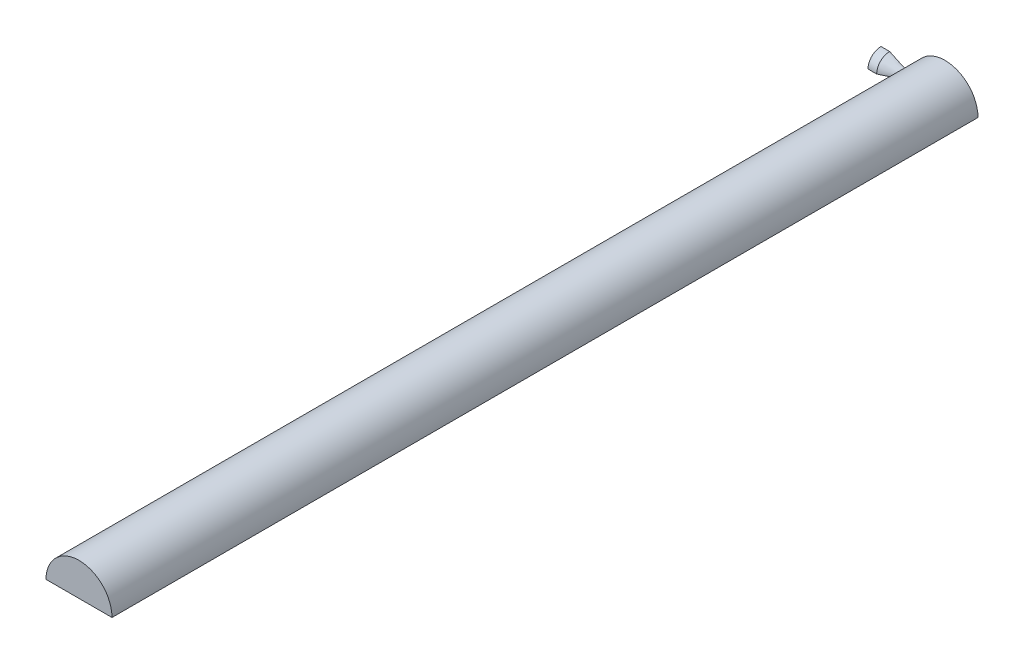
SolidWorks part; units mm, degrees
ref_plane "Front Plane" through (0, 0, 0) normal (0, 0, 1) x (1, 0, 0)
ref_plane "Top Plane" through (0, 0, 0) normal (0, 1, 0) x (1, 0, 0)
ref_plane "Right Plane" through (0, 0, 0) normal (1, 0, 0) x (0, 0, -1)
sketch "Sketch2" plane through (0, 0, 0) normal (0, 0, 1) x (1, 0, 0)
  line L0 (-0.6542, 15.02) -> (-10.6542, 15.02)
  line L1 (0, 0) -> (25.4, 0)
  line L3 (0, 0) -> (-10.6542, 0)
  line L4 (-10.6542, 15.02) -> (-10.6542, 0)
  line L5 (25.4, 4.5) -> (35.4, 4.5)
  line L6 (35.4, 4.5) -> (35.4, 0)
  line L7 (35.4, 0) -> (25.4, 0)
  spline S0 degree 4 poles (-3.1933, 16.2453) (-2.6483, 15.9818) (-1.017, 15.1947) (-0.2611, 14.8302) (2.741, 13.3865) (4.3471, 12.6191) (6.7016, 11.496) (8.6069, 10.5959) (10.7909, 9.5706) (12.8108, 8.6376) (14.9441, 7.6698) (16.9508, 6.7919) (18.7556, 6.0442) (20.2388, 5.4862) (21.3942, 5.1036) (22.2156, 4.8709) (22.897, 4.7103) (23.4645, 4.6056) (23.9541, 4.5381) (24.3543, 4.5036) (24.6693, 4.4888) (24.9186, 4.4854) (25.1247, 4.4882) (25.3381, 4.4959) (25.4828, 4.5045) (25.721, 4.5241) (25.9474, 4.5492) (26.1677, 4.5804) (26.3997, 4.6194) (26.7077, 4.6797) (27.1217, 4.7773) (27.4707, 4.8773) (27.7551, 4.9689) (27.9139, 5.0231) knots 0 0 0 0 0 0.083771 0.152014 0.220257 0.2885 0.356743 0.424986 0.493229 0.561472 0.629715 0.697958 0.757157 0.791278 0.819344 0.841894 0.858955 0.874283 0.887932 0.900719 0.906406 0.912093 0.917779 0.923466 0.929945 0.936423 0.942902 0.94938 0.956926 0.964472 0.980061 1 1 1 1 1 construction
  spline S1 degree 4 poles (-0.6542, 15.02) (-0.2198, 14.8107) (0.6106, 14.411) (2.741, 13.3865) (4.3471, 12.6191) (6.7016, 11.496) (8.6069, 10.5959) (10.7909, 9.5706) (12.8108, 8.6376) (14.9441, 7.6698) (16.9508, 6.7919) (18.7556, 6.0442) (20.2388, 5.4862) (21.3942, 5.1036) (22.2156, 4.8709) (22.897, 4.7103) (23.4645, 4.6056) (23.9541, 4.5381) (24.3543, 4.5036) (24.6693, 4.4888) (24.9186, 4.4854) (25.1247, 4.4882) (25.2794, 4.4938) (25.3599, 4.4977) (25.4, 4.5) knots 0.083771 0.083771 0.083771 0.083771 0.083771 0.152014 0.220257 0.2885 0.356743 0.424986 0.493229 0.561472 0.629715 0.697958 0.757157 0.791278 0.819344 0.841894 0.858955 0.874283 0.887932 0.900719 0.906406 0.912093 0.917779 0.923466 0.923466 0.923466 0.923466 0.923466
  point P8 (0, 0)
  dimension "D1" = 10.6542
  dimension "D2" = 15.02
  dimension "D3" = 4.5
  dimension "D4" = 25.4
  dimension "D5" = 10
revolve "Revolve3" add sketch "Sketch2" angle 90 about L1
sketch "TempLine" plane through (0, 0, 0) normal (0, 0, -1) x (-1, 0, 0)
  line L0 (-25.4, 4.5) -> (-25.4, 0)
  line L1 (10.6542, 0) -> (-35.4, 0) construction
sketch "Sketch11" plane through (0, 0, 0) normal (0, 0, 1) x (1, 0, 0)
  line L0 (25.1333, 0) -> (101.3333, 0)
  arc A0 (25.1333, 0) -> (101.3333, 0) centre (63.2333, 0) cw
  point P5 (0, 0)
  dimension "D2" = 38.1
  dimension "D1" = 76.2
extrude "Boss-Extrude2" add sketch "Sketch11" along normal blind 1000 contours A0 L0
